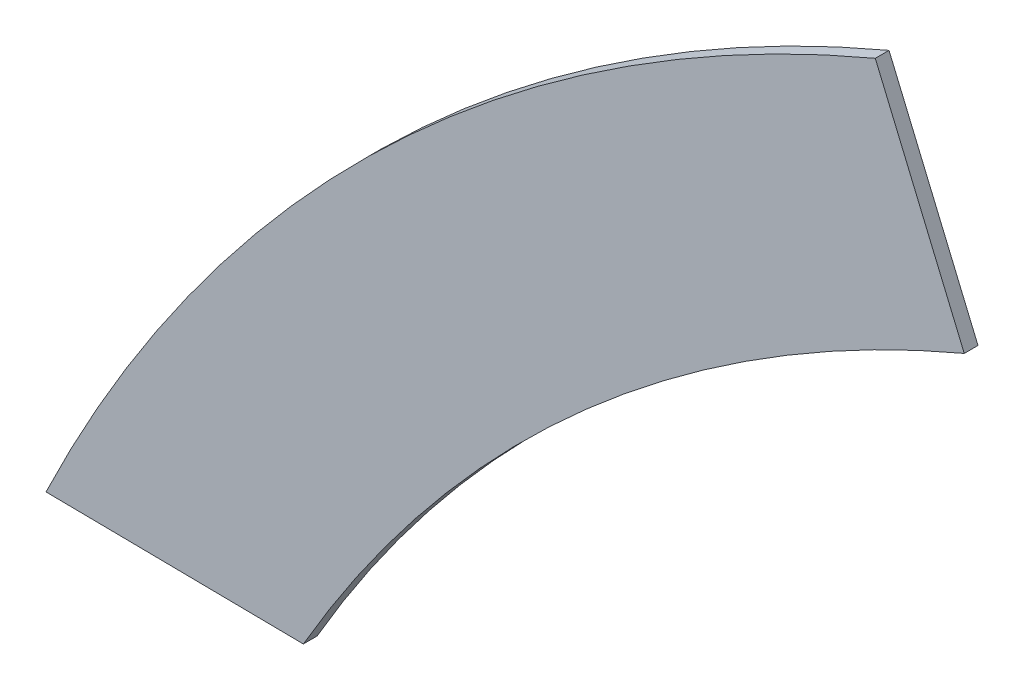
SolidWorks part; units mm, degrees
ref_plane "Ön Düzlem" through (0, 0, 0) normal (0, 0, 1) x (1, 0, 0)
ref_plane "Üst Düzlem" through (0, 0, 0) normal (0, 1, 0) x (1, 0, 0)
ref_plane "Sağ Düzlem" through (0, 0, 0) normal (1, 0, 0) x (0, 0, -1)
sketch "Çizim1" plane through (0, 0, 0) normal (0, 0, 1) x (1, 0, 0)
  line L0 (-539.9393, -342.935) -> (211.8139, 358.2528) construction
  line L1 (184.0359, 346.891) -> (261.717, 162.5932)
  line L2 (184.0359, 346.891) -> (145.942, 330.8345) construction
  line L3 (-539.9393, -342.935) -> (-315.2766, -345.5832)
  arc A0 (211.8139, 358.2528) -> (-539.9393, -342.935) centre (731.9022, -952.9176) ccw
  arc A1 (261.717, 162.5932) -> (-315.2766, -345.5832) centre (731.9022, -952.9176) ccw
  point P4 (184.0359, 346.891)
  dimension "D1" = 1028.0064
  dimension "D2" = 1000
  dimension "D3" = 90
extrude "Yükseklik-Ekstrüzyon1" add sketch "Çizim1" along normal blind 12 contours A1 L1 A0 L3
